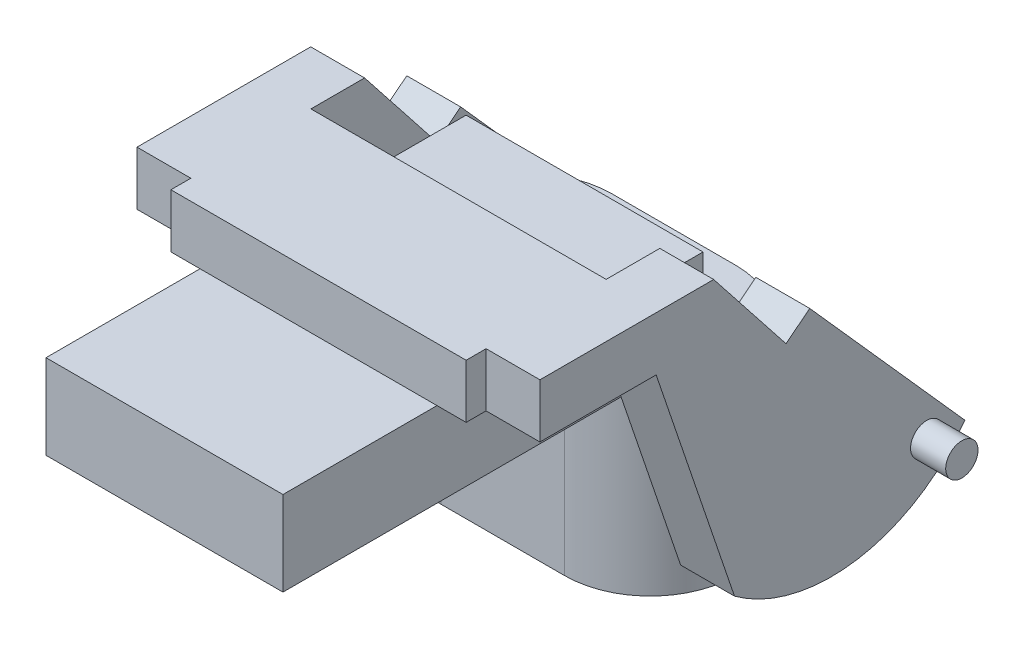
SolidWorks part; units mm, degrees
ref_plane "Płaszczyzna XY" through (0, 0, 0) normal (0, 0, 1) x (1, 0, 0)
ref_plane "Płaszczyzna XZ" through (0, 0, 0) normal (0, 1, 0) x (1, 0, 0)
ref_plane "Płaszczyzna YZ" through (0, 0, 0) normal (1, 0, 0) x (0, 0, -1)
sketch "Szkic1" plane through (0, 0, 0) normal (0, 1, 0) x (1, 0, 0)
  line L0 (-66.052, 72.7842) -> (-22.052, 72.7842)
  line L1 (-22.052, 72.7842) -> (-22.052, -5.2158)
  line L2 (-22.052, -5.2158) -> (-66.052, -5.2158)
  line L3 (-66.052, -5.2158) -> (-66.052, 72.7842)
  dimension "D1" = 44
  dimension "D2" = 78
extrude "Dodanie-wyciągnięcie1" add sketch "Szkic1" along normal blind 15.7 contours L1 L2 L3 L0
sketch "Szkic2" plane through (0, 15.7, 0) normal (0, 1, 0) x (1, 0, 0)
  line L0 (-44.052, 72.7842) -> (-44.052, -7.4072) construction
  line L2 (-16.642, 49.3842) -> (-71.462, 49.3842)
  line L3 (-71.462, 49.3842) -> (-71.462, 23.3842)
  line L4 (-71.462, 23.3842) -> (-16.642, 23.3842)
  line L5 (-22.052, -5.2158) -> (-66.052, -5.2158) construction
  line L6 (-66.052, 72.7842) -> (-22.052, 72.7842) construction
  line L7 (-16.642, 49.3842) -> (-16.642, 23.3842)
  point P8 (-44.052, -5.2158)
  point P12 (-44.052, 23.3842)
  point P13 (-44.052, 49.3842)
  dimension "D1" = 27.41
  dimension "D2" = 26
  dimension "D3" = 23.4
extrude "Dodanie-wyciągnięcie2" add sketch "Szkic2" along normal blind 10
sketch "Szkic3" plane through (0, 0, 0) normal (0, -1, 0) x (1, 0, 0)
  line L0 (-32.552, -89.3842) -> (-55.552, -89.3842)
  line L1 (-32.552, -57.5842) -> (-55.552, -57.5842)
  line L2 (-44.052, -101.4944) -> (-44.052, 49898.5056) construction
  line L5 (-66.052, -72.7842) -> (-22.052, -72.7842) construction
  arc A0 (-32.552, -57.5842) -> (-32.552, -89.3842) centre (-32.552, -73.4842) cw
  arc A2 (-55.552, -57.5842) -> (-55.552, -89.3842) centre (-55.552, -73.4842) ccw
  point P15 (-44.052, -57.5842)
  point P16 (-44.052, -89.3842)
  dimension "D2" = 15.9
  dimension "D1" = 23
  dimension "D3" = 16.6
extrude "Dodanie-wyciągnięcie3" add sketch "Szkic3" along normal blind 1 contours A0 L0 A2 L1
sketch "Szkic6" plane through (0, -1, 0) normal (0, -1, 0) x (-1, 0, 0)
  line L0 (44.052, 57.5842) -> (44.052, 82.6548) construction
  line L2 (32.552, 57.5842) -> (55.552, 57.5842) construction
  circle A0 centre (32.552, 73.4842) radius 4
  circle A1 centre (32.552, 73.4842) radius 10.4
  circle A2 centre (55.552, 73.4842) radius 10.4
  circle A3 centre (55.552, 73.4842) radius 4
  dimension "D2" = 8
  dimension "D3" = 20.8
  dimension "D1" = 11.5
  dimension "D4" = 15.9
extrude "Dodanie-wyciągnięcie4" add sketch "Szkic6" along normal blind 33
sketch "Szkic7" plane through (0, -1, 0) normal (0, -1, 0) x (-1, 0, 0)
  line L0 (44.052, -12.2694) -> (44.052, 72.9008) construction
  line L2 (55.552, 57.9842) -> (32.552, 57.9842)
  line L3 (55.552, 88.9842) -> (32.552, 88.9842)
  arc A0 (55.552, 57.9842) -> (55.552, 88.9842) centre (55.552, 73.4842) ccw
  circle A1 centre (55.552, 73.4842) radius 10.5
  arc A4 (32.552, 57.9842) -> (32.552, 88.9842) centre (32.552, 73.4842) cw
  circle A5 centre (32.552, 73.4842) radius 10.5
  point P13 (44.052, 53.4835)
  point P14 (44.052, 83.4849)
  point P16 (44.052, 88.9842)
  point P17 (44.052, 57.9842)
  dimension "D1" = 15.5
  dimension "D2" = 23
  dimension "D4" = 21
  dimension "D3" = 15.5
extrude "Dodanie-wyciągnięcie5" add sketch "Szkic7" along normal blind 33
sketch "Szkic8" plane through (0, -1, 0) normal (0, -1, 0) x (-1, 0, 0)
  line L0 (32.552, 57.5842) -> (55.552, 57.5842)
  line L1 (32.552, 57.5842) -> (55.552, 57.5842) construction
  line L2 (32.552, 89.3842) -> (55.552, 89.3842)
  line L3 (32.552, 89.3842) -> (55.552, 89.3842) construction
  line L4 (44.052, 89.3842) -> (44.052, 52.9972) construction
  line L5 (55.552, 57.7842) -> (32.552, 57.7842)
  line L6 (55.552, 89.1842) -> (32.552, 89.1842)
  arc A0 (55.552, 57.5842) -> (55.552, 89.3842) centre (55.552, 73.4842) ccw
  arc A1 (55.552, 57.5842) -> (55.552, 89.3842) centre (55.552, 73.4842) ccw construction
  arc A2 (32.552, 57.5842) -> (32.552, 89.3842) centre (32.552, 73.4842) cw
  arc A3 (55.552, 57.7842) -> (55.552, 89.1842) centre (55.552, 73.4842) ccw
  arc A4 (32.552, 57.7842) -> (32.552, 89.1842) centre (32.552, 73.4842) cw
  point P17 (44.052, 89.3842)
  point P19 (44.052, 57.5842)
  point P24 (44.052, 89.1842)
  point P25 (44.052, 57.7842)
  dimension "D1" = 15.7
extrude "Dodanie-wyciągnięcie6" add sketch "Szkic8" along normal blind 33
sketch "Szkic13" plane through (-16.642, 0, 0) normal (1, 0, 0) x (0, 0, -1)
  line L3 (63.2142, -27.159) -> (48.6629, 15.7)
  line L11 (89.3842, -34) -> (89.3842, 0) construction
  line L12 (49.3842, 15.7) -> (23.3842, 15.7) construction
  line L13 (48.6629, 15.7) -> (27.0903, 15.7)
  line L14 (27.0903, 15.7) -> (27.0903, 25.7)
  line L15 (23.3842, 25.7) -> (49.3842, 25.7) construction
  line L16 (27.0903, 25.7) -> (59.3474, 25.7)
  line L17 (59.3474, 25.7) -> (72.7842, 8.6596)
  line L19 (72.7842, 8.6596) -> (77.1844, 12.1292)
  line L20 (77.1844, 12.1292) -> (105.9842, -20.2395)
  arc A0 (105.9842, -20.2395) -> (63.2142, -27.159) centre (81.1888, -2.619) cw
  dimension "D7" = 30.4187
  dimension "D1" = 16.6
  dimension "D2" = 21.5726
  dimension "D3" = 32.2571
  dimension "D4" = 21.7008
  dimension "D5" = 5.6035
  dimension "D6" = 43.3263
  dimension "D8" = 45.2618
  dimension "D9" = 14.5513
  dimension "D10" = 13.4368
  dimension "D11" = 54.0984
extrude "Dodanie-wyciągnięcie22" add sketch "Szkic13" along normal blind 10
sketch "Szkic14" plane through (0, -34, 0) normal (0, -1, 0) x (-1, 0, 0)
  line L0 (44.052, 88.9842) -> (44.052, 57.9842) construction
  line L1 (55.552, 88.9842) -> (32.552, 88.9842) construction
  line L2 (32.552, 57.9842) -> (55.552, 57.9842) construction
ref_plane "Płaszczyzna3" through (-44.052, 0, 0) normal (1, 0, 0) x (0, 0, -1)
mirror "Lustro2" about plane through (-44.052, 0, 0) normal (1, 0, 0) of "Dodanie-wyciągnięcie22"
sketch "Szkic15" plane through (-6.642, 0, 0) normal (1, 0, 0) x (0, 0, -1)
  circle A0 centre (98.9035, -19.7432) radius 3
  dimension "D1" = 6
  dimension "D2" = 98.9035
  dimension "D3" = 19.7432
extrude "Dodanie-wyciągnięcie23" add sketch "Szkic15" along normal blind 6.525 contours A0
mirror "Lustro3" about plane through (-44.052, 0, 0) normal (1, 0, 0) of "Dodanie-wyciągnięcie23"
